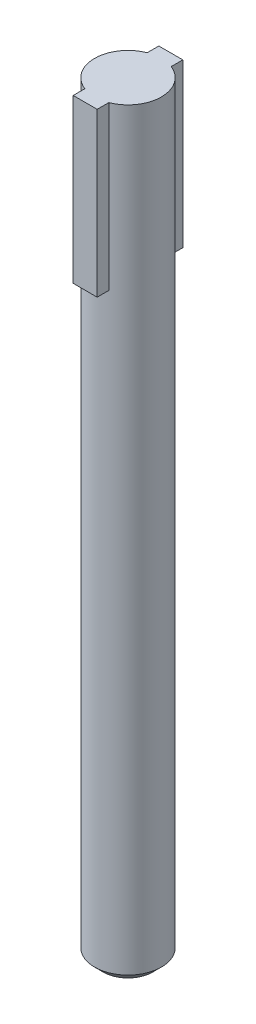
SolidWorks part; units mm, degrees
material "PLA personnalisé"
ref_plane "Plan de face" through (0, 0, 0) normal (0, 0, 1) x (1, 0, 0)
ref_plane "Plan de dessus" through (0, 0, 0) normal (0, 1, 0) x (1, 0, 0)
ref_plane "Plan de droite" through (0, 0, 0) normal (1, 0, 0) x (0, 0, -1)
sketch "Esquisse1" plane through (0, 0, 0) normal (0, 1, 0) x (1, 0, 0)
  circle A0 centre (0, 0) radius 3.9
  dimension "D1" = 7.8
extrude "Boss.-Extru.1" add sketch "Esquisse1" along normal blind 8 and the other way blind 81
sketch "Esquisse2" plane through (0, 8, 0) normal (0, 1, 0) x (1, 0, 0)
  line L0 (-1.4, 0) -> (1.4, 0)
  line L1 (1.4, 5) -> (1.4, -5)
  line L2 (1.4, -5) -> (-1.4, -5)
  line L3 (-1.4, -5) -> (-1.4, 5)
  line L4 (1.4, 5) -> (-1.4, 5)
  circle M5 centre (0, 0) radius 3.9
  dimension "D1" = 1.4
  dimension "D2" = 2.8
  dimension "D3" = 5
extrude "Boss.-Extru.2" add sketch "Esquisse2" against normal blind 19 contours L1 L4 L3 M5 | L3 L2 L1 M5 | L3 L1 L0 M5 | L3 L0 L1 M5
chamfer "Chanfrein1" distance 1 angle 45 1 edges at (0, -81, 3.9)
